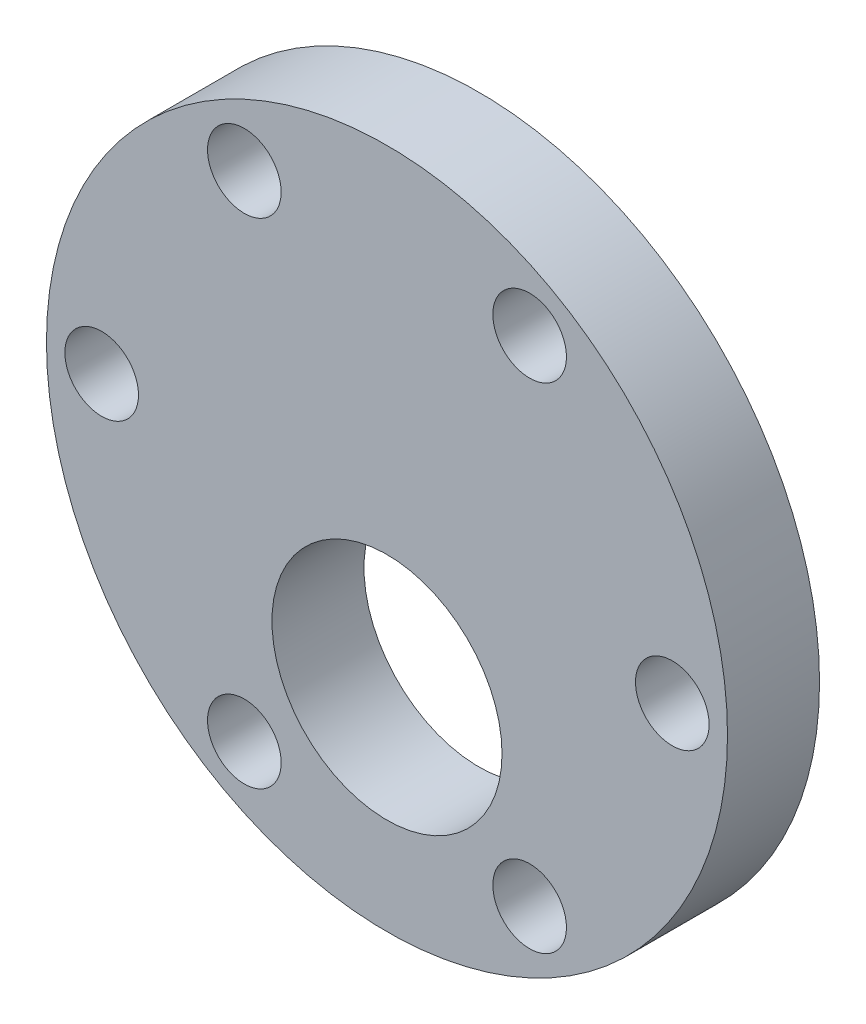
SolidWorks part; units mm, degrees
ref_plane "Plan de face" through (0, 0, 0) normal (0, 0, 1) x (1, 0, 0)
ref_plane "Plan de dessus" through (0, 0, 0) normal (0, 1, 0) x (1, 0, 0)
ref_plane "Plan de droite" through (0, 0, 0) normal (1, 0, 0) x (0, 0, -1)
sketch "Esquisse1" plane through (0, 0, 0) normal (0, 0, 1) x (1, 0, 0)
  circle A0 centre (0, 0) radius 18.5
  dimension "D1" = 37
extrude "Boss.-Extru.1" add sketch "Esquisse1" along normal blind 5
sketch "Esquisse2" plane through (0, 0, 5) normal (0, 0, 1) x (1, 0, 0)
  line L0 (-18.5, 0) -> (18.5, 0) construction
  circle A0 centre (0, 0) radius 18.5 construction
  circle A1 centre (-15.5, 0) radius 2
  circle A2 centre (15.5, 0) radius 2
  circle A3 centre (7.75, -13.4234) radius 2
  circle A4 centre (-7.75, -13.4234) radius 2
  circle A5 centre (-15.5, 0) radius 2
  circle A6 centre (-7.75, 13.4234) radius 2
  circle A7 centre (7.75, 13.4234) radius 2
  point P22 (0, 0)
  dimension "D1" = 31
  dimension "D2" = 15.5
  dimension "D3" = 4
  dimension "D4" = 4
  dimension "D5" = 6
extrude "Enlèv. mat.-Extru.1" cut sketch "Esquisse2" against normal through all contours A6 | A7 | A2 L0 | L0 A2 | A3 | A4 | L0 A5 | A1 L0
sketch "Esquisse3" plane through (0, 0, 5) normal (0, 0, 1) x (1, 0, 0)
  circle A0 centre (0, -7) radius 6.25
  dimension "D1" = 12.5
  dimension "D3" = 7
extrude "Enlèv. mat.-Extru.2" cut sketch "Esquisse3" against normal through all
